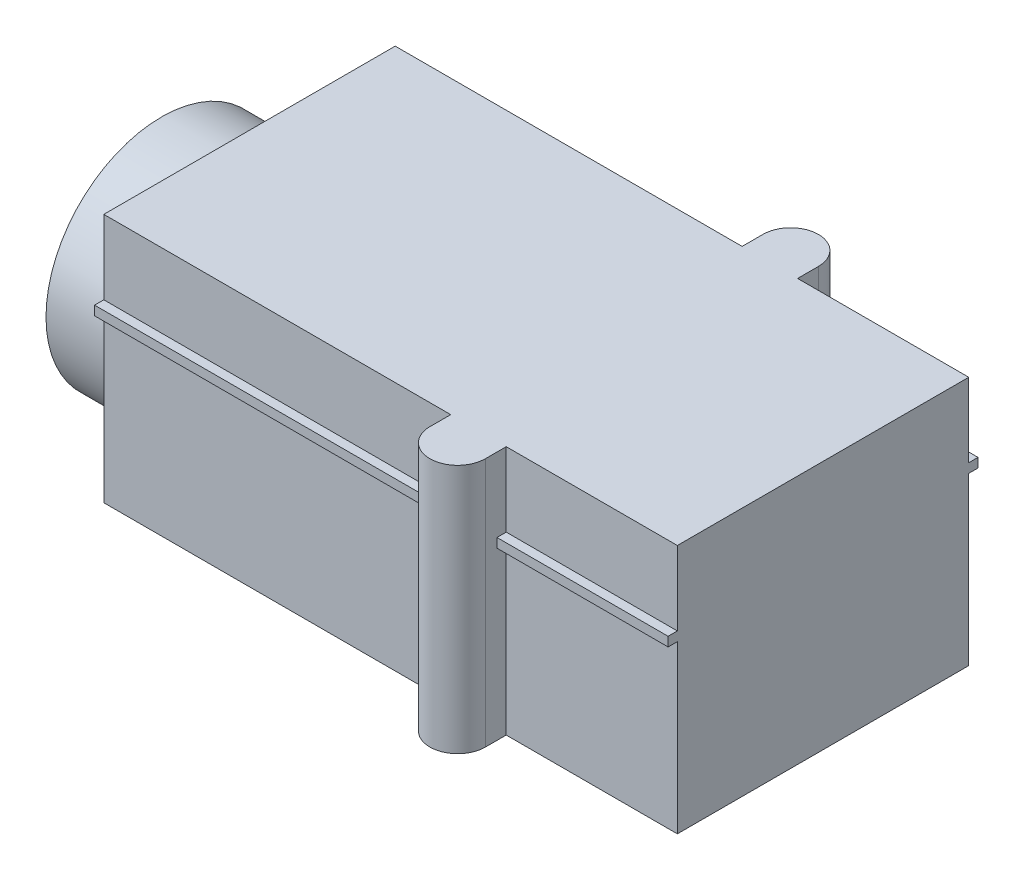
SolidWorks part; units mm, degrees
ref_plane "Front Plane" through (0, 0, 0) normal (0, 0, 1) x (1, 0, 0)
ref_plane "Top Plane" through (0, 0, 0) normal (0, 1, 0) x (1, 0, 0)
ref_plane "Right Plane" through (0, 0, 0) normal (1, 0, 0) x (0, 0, -1)
sketch "Sketch1" plane through (0, 0, 0) normal (0, 1, 0) x (1, 0, 0)
  line L0 (0, -3.15) -> (0, 3.15)
  line L1 (0, 3.15) -> (7.5, 3.15)
  line L2 (12.4, 3.15) -> (12.4, -3.15)
  line L3 (12.4, -3.15) -> (8.7, -3.15)
  line L4 (7.5, 3.15) -> (7.5, 3.6)
  line L5 (7.5, -3.15) -> (0, -3.15)
  line L6 (8.7, 3.6) -> (8.7, 3.15)
  line L7 (7.5, -3.15) -> (7.5, -3.6)
  line L8 (11.2269, 4.2) -> (11.8803, 4.2) construction
  line L9 (8.7, -3.6) -> (8.7, -3.15)
  line L10 (8.7, 3.15) -> (12.4, 3.15)
  line L11 (11.2269, -4.2) -> (12.1537, -4.2) construction
  arc A0 (7.5, 3.6) -> (8.7, 3.6) centre (8.1, 3.6) cw
  arc A1 (8.7, -3.6) -> (7.5, -3.6) centre (8.1, -3.6) cw
  dimension "D1" = 6.3
  dimension "D2" = 1.2
  dimension "D3" = 4.2
  dimension "D4" = 4.2
  dimension "D5" = 8.1
  dimension "D6" = 12.4
extrude "Boss-Extrude1" add sketch "Sketch1" along normal blind 5.4
sketch "Sketch2" plane through (0, 0, 0) normal (-1, 0, 0) x (0, 0, 1)
  line L0 (-3.15, 0) -> (3.15, 0) construction
  circle A0 centre (0, 2.2) radius 2.5
  dimension "D2" = 5
  dimension "D1" = 2.2
extrude "Boss-Extrude2" add sketch "Sketch2" along normal blind 1.9
ref_plane "Plane1" through (0, 3.6, 0) normal (0, -1, 0) x (-1, 0, 0)
sketch "Sketch3" plane through (0, 3.6, 0) normal (0, -1, 0) x (-1, 0, 0)
  line L0 (0, 3.15) -> (0, -3.15) construction
  line L1 (0, 3.35) -> (-12.4, 3.35)
  line L2 (0, 3.35) -> (0, -3.35)
  line L3 (0, -3.35) -> (-12.4, -3.35)
  line L4 (-12.4, 3.35) -> (-12.4, -3.35)
  line L5 (-12.4, -3.15) -> (-12.4, 3.15) construction
  line L6 (-7.5, 3.15) -> (0, 3.15) construction
  dimension "D1" = 0.2
extrude "Boss-Extrude3" add sketch "Sketch3" against normal blind 0.2
